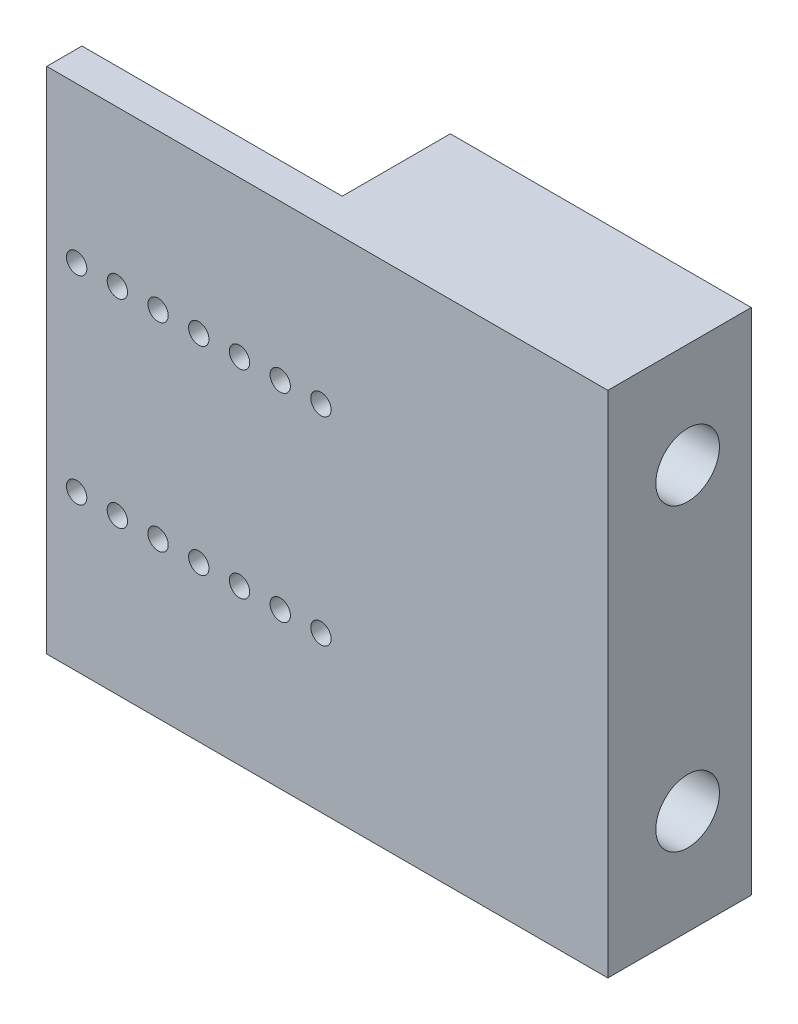
SolidWorks part; units mm, degrees
ref_plane "Alzado" through (0, 0, 0) normal (0, 0, 1) x (1, 0, 0)
ref_plane "Planta" through (0, 0, 0) normal (0, 1, 0) x (1, 0, 0)
ref_plane "Vista lateral" through (0, 0, 0) normal (1, 0, 0) x (0, 0, -1)
sketch "Croquis1" plane through (0, 0, 0) normal (0, 0, 1) x (1, 0, 0)
  line L8 (88.2, 0) -> (88.2, 37.6)
  line L11 (0, 37.6) -> (0, 0)
  line L12 (0, 37.6) -> (0, 58.8)
  line L13 (0, 0) -> (0, -21.2)
  line L14 (0, 58.8) -> (88.2, 58.8)
  line L15 (88.2, 58.8) -> (88.2, 37.6)
  line L16 (0, -21.2) -> (88.2, -21.2)
  line L17 (88.2, -21.2) -> (88.2, 0)
  circle A0 centre (4.7, 34.4) radius 1.6
  circle A2 centre (11.1, 34.4) radius 1.6
  circle A3 centre (17.5, 34.4) radius 1.6
  circle A4 centre (23.9, 34.4) radius 1.6
  circle A5 centre (30.3, 34.4) radius 1.6
  circle A6 centre (36.7, 34.4) radius 1.6
  circle A8 centre (43.1, 34.4) radius 1.6
  circle A9 centre (43.1, 3.2) radius 1.6
  circle A10 centre (36.7, 3.2) radius 1.6
  circle A11 centre (30.3, 3.2) radius 1.6
  circle A12 centre (23.9, 3.2) radius 1.6
  circle A13 centre (17.5, 3.2) radius 1.6
  circle A14 centre (11.1, 3.2) radius 1.6
  circle A15 centre (4.7, 3.2) radius 1.6
extrude "Saliente-Extruir3" add sketch "Croquis1" along normal blind 7.54
sketch "Croquis3" plane through (0, 0, 0) normal (0, 0, -1) x (-1, 0, 0)
  line L0 (-88.2, -21.2) -> (-39.9, -21.2)
  line L1 (0, -21.2) -> (-88.2, -21.2) construction
  line L2 (-88.2, 58.8) -> (-39.9, 58.8)
  line L3 (-88.2, 58.8) -> (0, 58.8) construction
  line L4 (-39.9, -21.2) -> (-39.9, 58.8)
  line L5 (-88.2, -21.2) -> (-88.2, 58.8)
extrude "Saliente-Extruir4" add sketch "Croquis3" along normal blind 15
sketch "Croquis5" plane through (39.9, 0, 0) normal (-1, 0, 0) x (0, 0, 1)
  circle A0 centre (-5, 42.36) radius 5
  circle A1 centre (-5, -4.76) radius 5
sketch "Croquis6" plane through (0, 0, 0) normal (-1, 0, 0) x (0, 0, 1)
  line L0 (0, 58.8) -> (2, 58.8)
  line L2 (7.54, 58.8) -> (0, 58.8) construction
  line L3 (2, 58.8) -> (2, -21.2)
  line L4 (7.54, -21.2) -> (0, -21.2) construction
  line L5 (2, -21.2) -> (0, -21.2)
  line L7 (0, 58.8) -> (-15, 58.8)
  line L8 (-15, 58.8) -> (-15, -21.2)
  line L9 (-15, -21.2) -> (0, -21.2)
extrude "Cortar-Extruir1" cut sketch "Croquis6" against normal blind 40.9
extrude "Cortar-Extruir2" cut sketch "Croquis5" against normal blind 54.9
